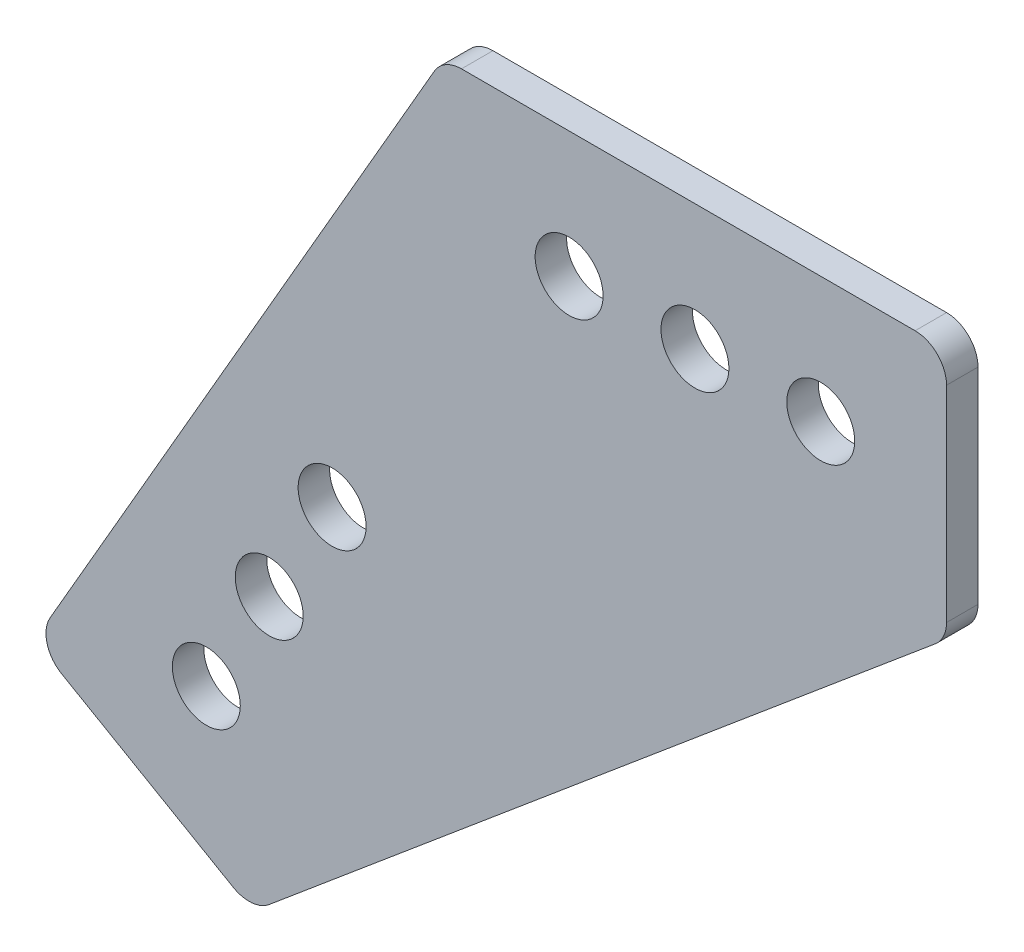
SolidWorks part; units mm, degrees
ref_plane "Front Plane" through (0, 0, 0) normal (0, 0, 1) x (1, 0, 0)
ref_plane "Top Plane" through (0, 0, 0) normal (0, 1, 0) x (1, 0, 0)
ref_plane "Right Plane" through (0, 0, 0) normal (1, 0, 0) x (0, 0, -1)
sketch "Sketch1" plane through (0, 0, 0) normal (0, 0, 1) x (1, 0, 0)
  line L0 (0, 0) -> (50.8, 0)
  line L1 (0, 0) -> (-41.275, -71.4904)
  line L4 (50.8, -25.4) -> (50.8, 0)
  line L5 (-19.278, -84.1904) -> (-41.275, -71.4904)
  line L6 (-30.2765, -77.8404) -> (7.3323, -12.7) construction
  line L7 (50.8, -12.7) -> (7.3323, -12.7) construction
  line L8 (-19.278, -84.1904) -> (50.8, -25.4)
  circle A0 centre (38.1, -12.7) radius 3.429
  circle A1 centre (25.4, -12.7) radius 3.429
  circle A2 centre (12.7, -12.7) radius 3.429
  circle A3 centre (-23.9265, -66.8419) radius 3.429
  circle A4 centre (-17.5765, -55.8434) radius 3.429
  circle A5 centre (-11.2265, -44.8448) radius 3.429
  point P3 (-20.2141, -83.6499)
  point P19 (50.8, -24.2259)
  dimension "D5" = 6.858
  dimension "D6" = 12.7
  dimension "D8" = 12.7
  dimension "D9" = 12.7
  dimension "D11" = 12.7
  dimension "D1" = 50.8
  dimension "D2" = 82.55
  dimension "D3" = 120
  dimension "D12" = 25.4
  dimension "D4" = 25.4
  dimension "D7" = 3
  dimension "D10" = 3
extrude "Boss-Extrude1" add sketch "Sketch1" along normal blind 3.175
fillet "Fillet1" radius 3.175 5 edges at (-41.275, -71.4904, 1.5875) (-19.278, -84.1904, 1.5875) (50.8, -25.4, 1.5875) (50.8, 0, 1.5875) (0, 0, 1.5875)
